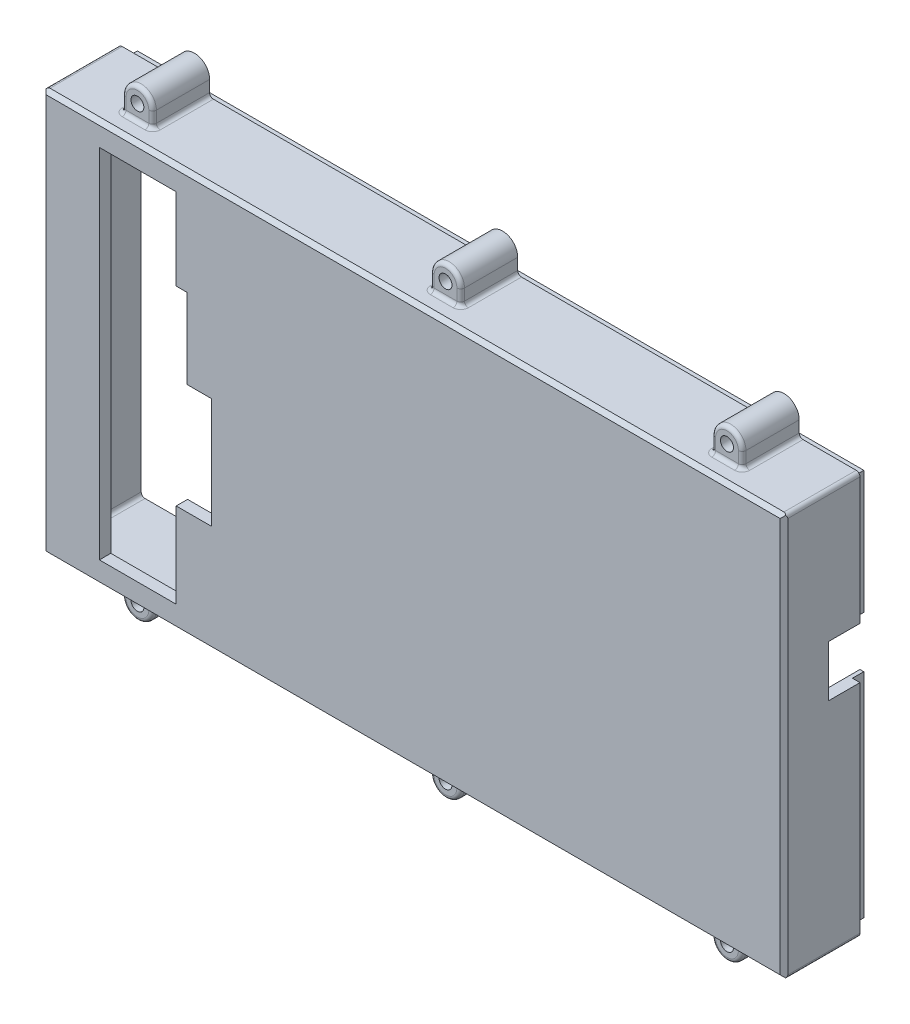
SolidWorks part; units mm, degrees
ref_plane "Front Plane" through (0, 0, 0) normal (0, 0, 1) x (1, 0, 0)
ref_plane "Top Plane" through (0, 0, 0) normal (0, 1, 0) x (1, 0, 0)
ref_plane "Right Plane" through (0, 0, 0) normal (1, 0, 0) x (0, 0, -1)
sketch "Sketch1" plane through (0, 0, 0) normal (0, 0, 1) x (1, 0, 0)
  line L0 (-85.075, -57) -> (-85.075, -53)
  line L1 (-101.075, 53) -> (-85.075, 53)
  line L2 (-101.075, 53) -> (-101.075, -53)
  line L3 (-101.075, -53) -> (-85.075, -53)
  line L4 (94.075, 53) -> (94.075, -53)
  line L5 (-77.075, -57) -> (-77.075, -53)
  line L6 (-4, -57) -> (-4, -53)
  line L7 (4, -57) -> (4, -53)
  line L8 (70.075, -57) -> (70.075, -53)
  line L9 (130.7802, 0) -> (-134.8825, 0) construction
  line L10 (78.075, -57) -> (78.075, -53)
  line L11 (4, -53) -> (70.075, -53)
  line L12 (-77.075, -53) -> (-4, -53)
  line L13 (78.075, -53) -> (94.075, -53)
  line L14 (78.075, 57) -> (78.075, 53)
  line L15 (70.075, 57) -> (70.075, 53)
  line L16 (4, 57) -> (4, 53)
  line L17 (-4, 57) -> (-4, 53)
  line L18 (-77.075, 57) -> (-77.075, 53)
  line L19 (-85.075, 57) -> (-85.075, 53)
  line L20 (-77.075, 53) -> (-4, 53)
  line L21 (4, 53) -> (70.075, 53)
  line L22 (78.075, 53) -> (94.075, 53)
  arc A0 (-85.075, -57) -> (-77.075, -57) centre (-81.075, -57) ccw
  arc A1 (70.075, -57) -> (78.075, -57) centre (74.075, -57) ccw
  arc A2 (-4, -57) -> (4, -57) centre (0, -57) ccw
  arc A3 (70.075, 57) -> (78.075, 57) centre (74.075, 57) cw
  arc A4 (-4, 57) -> (4, 57) centre (0, 57) cw
  arc A5 (-85.075, 57) -> (-77.075, 57) centre (-81.075, 57) cw
  point P4 (0, -61)
  point P6 (-101.075, 0)
  dimension "D3" = 8
  dimension "D1" = 94.075
  dimension "D2" = 106
  dimension "D4" = 20
  dimension "D5" = 20
  dimension "D6" = 101.075
extrude "Boss-Extrude2" add sketch "Sketch1" along normal blind 20
sketch "Sketch3" plane through (0, 0, 0) normal (0, 0, -1) x (-1, 0, 0)
  line L0 (101.075, -53) -> (85.075, -53) construction
  line L1 (98.075, -50) -> (-91.075, -50)
  line L2 (98.075, -50) -> (98.075, 50)
  line L3 (98.075, 50) -> (-91.075, 50)
  line L4 (-91.075, -50) -> (-91.075, 50)
  line L5 (101.075, 53) -> (101.075, -53) construction
  line L7 (-94.075, -53) -> (-94.075, 53) construction
  point P7 (98.075, 0)
  dimension "D1" = 3
  dimension "D2" = 3
  dimension "D3" = 3
extrude "Cut-Extrude2" cut sketch "Sketch3" against normal offset from surface (17 mm away) 3 up to face at (-2.5, 0, 20)
sketch "Sketch13" plane through (0, 0, 17) normal (0, 0, -1) x (-1, 0, 0)
  line L1 (-92.075, 51) -> (99.075, 51)
  line L2 (-92.075, 51) -> (-92.075, -51)
  line L3 (-92.075, -51) -> (99.075, -51)
  line L4 (99.075, 51) -> (99.075, -51)
  line L7 (101.075, 53) -> (101.075, -53) construction
  line L8 (77.075, -53) -> (4, -53) construction
  line L9 (-94.075, -53) -> (-94.075, 53) construction
  line L10 (98.075, 50) -> (-91.075, 50) construction
  line L11 (98.075, 50) -> (-91.075, 50)
  line L12 (98.075, 50) -> (98.075, -50)
  line L13 (98.075, -50) -> (-91.075, -50)
  line L14 (-91.075, 50) -> (-91.075, -50)
  line L15 (98.075, -50) -> (98.075, 50) construction
  point P6 (-92.075, 0)
  dimension "D1" = 2
  dimension "D2" = 2
  dimension "D3" = 2
sketch "Sketch22" plane through (0, 0, 20) normal (0, 0, 1) x (1, 0, 0)
  line L0 (-77.075, -53) -> (-4, -53) construction
  line L1 (-101.075, -73) -> (94.075, -73)
  line L2 (-101.075, -73) -> (-101.075, -53)
  line L3 (-101.075, -53) -> (94.075, -53)
  line L4 (94.075, -73) -> (94.075, -53)
  line L5 (-101.075, 73) -> (94.075, 73)
  line L6 (-101.075, 73) -> (-101.075, 53)
  line L7 (-101.075, 53) -> (94.075, 53)
  line L8 (94.075, 73) -> (94.075, 53)
  line L11 (-85.075, 53) -> (-101.075, 53) construction
  line L12 (-101.075, 53) -> (-101.075, -53) construction
  line L13 (94.075, -53) -> (94.075, 53) construction
  point P16 (0, 0)
  point P17 (0, 0)
  point P18 (0, 0)
  point P19 (0, 0)
  dimension "D1" = 20
  dimension "D2" = 20
extrude "Cut-Extrude8" cut sketch "Sketch22" against normal blind 5
chamfer "Chamfer1" distance 1 angle 45 4 edges at (-101.075, 0, 20) (-3.5, 53, 20) (94.075, 0, 20) (-3.5, -53, 20)
hole_wizard "M3 Clearance Hole1" positions "Sketch19" profile "Sketch20" hole size "M3" standard "ANSI Metric" end condition through all
sketch "Sketch19" plane through (0, 0, 0) normal (0, 0, -1) x (-1, 0, 0)
  point P0 (81.075, -57)
  point P3 (0, -57)
  point P6 (81.075, 57)
  point P9 (0, 57)
  point P12 (-74.075, 57)
  point P15 (-74.075, -57)
sketch "Sketch20" plane through (-81.075, -57, 0) normal (1, 0, 0) x (0, 1, 0)
  line L0 (0, 0) -> (0, 20)
  line L1 (0, 20) -> (1.7, 20)
  line L2 (1.7, 20) -> (1.7, 0)
  line L5 (1.7, 0) -> (0, 0)
  line L11 (0, -6.35) -> (0, 107.95) construction
  dimension "Thru Hole Dia." = 3.4
  dimension "Thru Hole Depth" = 20
extrude "Boss-Extrude3" add sketch "Sketch13" along normal blind 20
sketch "Sketch18" plane through (94.075, 0, 0) normal (1, 0, 0) x (0, 0, -1)
  line L0 (0, 51) -> (0, -51) construction
  line L1 (6.25, 18.61) -> (-8.25, 18.61)
  line L2 (6.25, 18.61) -> (6.25, 5.11)
  line L3 (6.25, 5.11) -> (-8.25, 5.11)
  line L4 (-8.25, 18.61) -> (-8.25, 5.11)
  point P4 (6.25, 11.86)
  point P6 (-1, 18.61)
  dimension "D1" = 11.86
  dimension "D2" = 1
  dimension "D3" = 13.5
  dimension "D4" = 14.5
extrude "Cut-Extrude4" cut sketch "Sketch18" against normal blind 20
fillet "Fillet1" radius 1 44 edges at (-101.075, -53, 9.5) (-101.075, 53, 9.5) (-85.075, 53, 7.5) (-4, 53, 7.5) (70.075, 53, 7.5) (78.075, -53, 7.5) (4, -53, 7.5) (-77.075, -53, 7.5) (-85.075, -53, 7.5) (-4, -53, 7.5) (70.075, -53, 7.5) (91.075, 50, 7) (91.075, -50, 7) (-98.075, 50, 7) (-98.075, -50, 7) (94.075, -53, 9.5) (94.075, 53, 9.5) (78.075, 53, 7.5) (4, 53, 7.5) (-77.075, 53, 7.5) (-85.075, -55, 15) (-81.075, -53, 15) (-77.075, -55, 15) (-81.075, -61, 15) (-4, -55, 15) (0, -53, 15) (4, -55, 15) (0, -61, 15) (70.075, -55, 15) (74.075, -53, 15) (78.075, -55, 15) (74.075, -61, 15) (-81.075, 53, 15) (-85.075, 55, 15) (-81.075, 61, 15) (-77.075, 55, 15) (0, 53, 15) (-4, 55, 15) (0, 61, 15) (4, 55, 15) (74.075, 53, 15) (70.075, 55, 15) (74.075, 61, 15) (78.075, 55, 15)
sketch "Sketch21" plane through (0, 0, 17) normal (0, 0, -1) x (-1, 0, 0)
  line L0 (101.075, 52) -> (101.075, -52) construction
  line L1 (86.075, -47) -> (65.875, -47)
  line L2 (86.075, -47) -> (86.075, 47)
  line L3 (86.075, 47) -> (65.875, 47)
  line L4 (65.875, -47) -> (65.875, -24.6)
  line L5 (76.075, -53) -> (5, -53) construction
  line L6 (5, 53) -> (76.075, 53) construction
  line L7 (65.875, 25.5) -> (65.875, 47)
  line L8 (65.875, -24.6) -> (56.575, -24.6)
  line L9 (63.075, 4.5) -> (56.575, 4.5)
  line L11 (56.575, -24.6) -> (56.575, 4.5)
  line L14 (65.875, 25.5) -> (63.075, 25.5)
  line L15 (63.075, 4.5) -> (63.075, 25.5)
  dimension "D1" = 15
  dimension "D2" = 6
  dimension "D3" = 6
  dimension "D4" = 35.2
  dimension "D5" = 28.4
  dimension "D6" = 44.5
  dimension "D7" = 23
  dimension "D8" = 27.5
  dimension "D9" = 57.5
extrude "Cut-Extrude7" cut sketch "Sketch21" against normal blind 10
